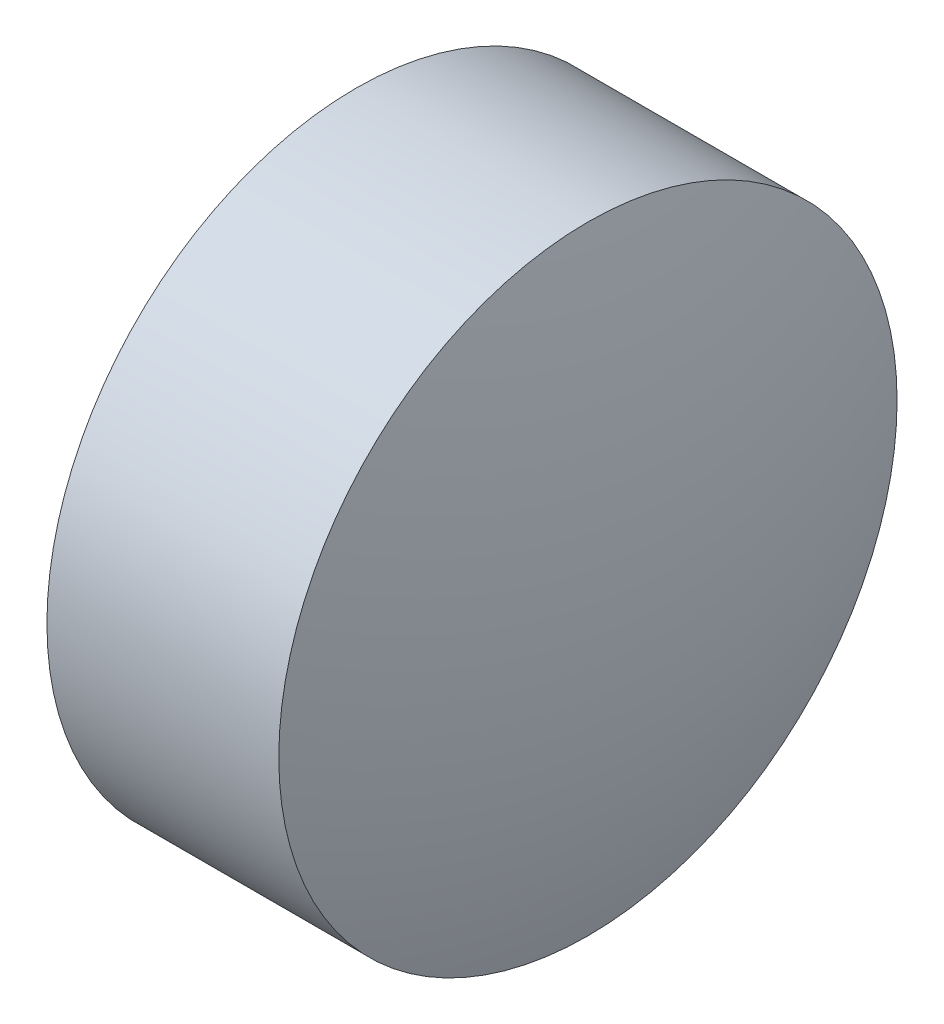
SolidWorks part; units mm, degrees
ref_plane "前视基准面" through (0, 0, 0) normal (0, 0, 1) x (1, 0, 0)
ref_plane "上视基准面" through (0, 0, 0) normal (0, 1, 0) x (1, 0, 0)
ref_plane "右视基准面" through (0, 0, 0) normal (1, 0, 0) x (0, 0, -1)
sketch "草图1" plane through (0, 0, 0) normal (0, 0, 1) x (1, 0, 0)
  line L0 (382.5386, 60.2049) -> (385.2361, 60.2049) construction
  line L1 (382.9667, 60.2049) -> (382.9667, 62.2049)
  line L2 (384.7667, 60.2049) -> (382.9667, 60.2049)
  line L5 (382.9667, 62.2049) -> (384.4667, 62.2049)
  arc A0 (384.7667, 60.2049) -> (384.4667, 62.2049) centre (377.95, 60.2049) ccw
revolve "旋转1" add sketch "草图1" angle 360 about L0
